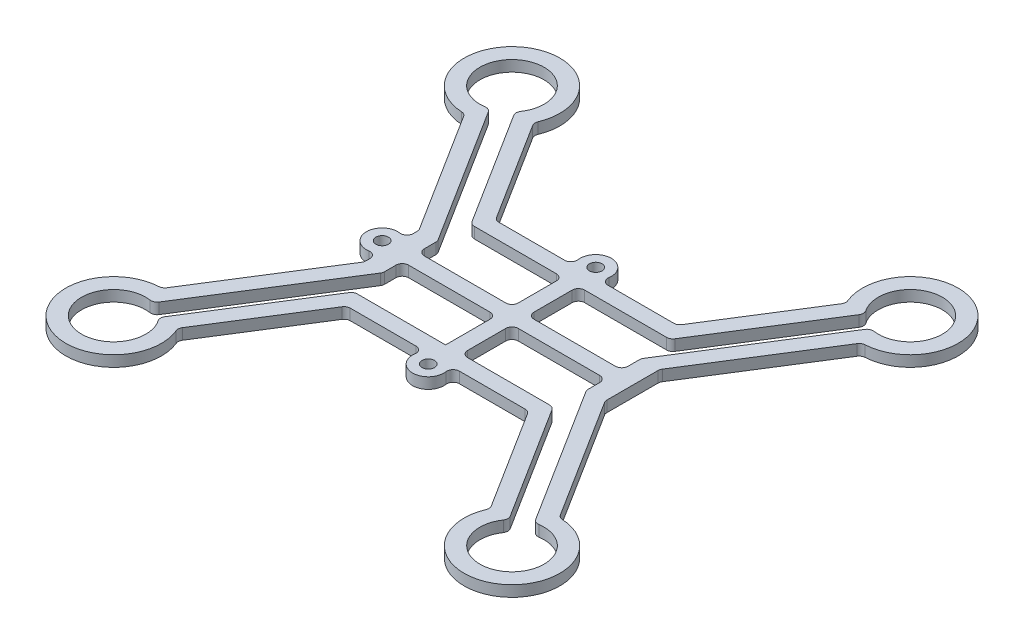
SolidWorks part; units mm, degrees
material "Hexcel AS4C (3000 Filaments)"
ref_plane "Front Plane" through (0, 0, 0) normal (0, 0, 1) x (1, 0, 0)
ref_plane "Top Plane" through (0, 0, 0) normal (0, 1, 0) x (1, 0, 0)
ref_plane "Right Plane" through (0, 0, 0) normal (1, 0, 0) x (0, 0, -1)
sketch "Sketch1" plane through (0, 0, 0) normal (0, 1, 0) x (1, 0, 0)
  line L0 (0, 28.7416) -> (0, -31.95) construction
  line L1 (-19.25, 11.875) -> (19.25, 11.875)
  line L2 (-19.25, 11.875) -> (-19.25, -11.875)
  line L3 (-19.25, -11.875) -> (19.25, -11.875)
  line L4 (19.25, 11.875) -> (19.25, -11.875)
  line L5 (-19.25, 11.875) -> (19.25, -11.875) construction
  line L6 (-19.25, -11.875) -> (19.25, 11.875) construction
  line L7 (-23.7954, 0) -> (45.7192, 0) construction
  line L8 (-31.8198, 4.3198) -> (-31.8198, -4.3198) construction
  line L9 (-31.8198, -31.8198) -> (-31.8198, 31.8198) construction
  line L10 (-31.8198, 31.8198) -> (-19.25, 11.875) construction
  line L11 (19.25, 9.825) -> (-13.5, 9.825)
  line L12 (19.25, 9.825) -> (19.25, -9.825)
  line L13 (19.25, -9.825) -> (-13.5, -9.825)
  line L14 (-13.5, 9.825) -> (-13.5, -9.825)
  line L15 (19.25, 9.825) -> (-13.5, -9.825) construction
  line L16 (19.25, -9.825) -> (-13.5, 9.825) construction
  line L17 (-31.727, 24.1704) -> (-19.25, 4.3728)
  line L18 (-24.959, 28.4358) -> (-14.5219, 11.875)
  line L19 (-35.2038, 29.6871) -> (-22.634, 9.7423) construction
  line L20 (-28.4358, 33.9525) -> (-15.866, 14.0077) construction
  line L21 (24.959, 28.4358) -> (14.5219, 11.875)
  line L22 (31.727, 24.1704) -> (19.25, 4.3728)
  line L23 (24.959, -28.4358) -> (14.5219, -11.875)
  line L24 (31.727, -24.1704) -> (19.25, -4.3728)
  line L25 (-24.959, -28.4358) -> (-14.5219, -11.875)
  line L26 (-31.727, -24.1704) -> (-19.25, -4.3728)
  line L27 (-31.8198, 31.8198) -> (31.8198, 31.8198) construction
  circle A0 centre (-31.8198, 31.8198) radius 27.5
  circle A1 centre (31.8198, 31.8198) radius 27.5
  circle A2 centre (-31.8198, -31.8198) radius 27.5
  circle A3 centre (31.8198, -31.8198) radius 27.5
  circle A4 centre (-31.8198, 31.8198) radius 7.65
  circle A5 centre (-31.8198, 31.8198) radius 5.125
  circle A6 centre (31.8198, 31.8198) radius 5.125
  circle A7 centre (31.8198, 31.8198) radius 7.65
  circle A8 centre (31.8198, -31.8198) radius 5.125
  circle A9 centre (31.8198, -31.8198) radius 7.65
  circle A10 centre (-31.8198, -31.8198) radius 5.125
  circle A11 centre (-31.8198, -31.8198) radius 7.65
  point P0 (0, 0)
  point P18 (2.875, 0)
  dimension "D3" = 55
  dimension "D8" = 15.3
  dimension "D9" = 10.25
  dimension "D1" = 23.75
  dimension "D2" = 38.5
  dimension "D4" = 19.65
  dimension "D5" = 32.75
  dimension "D10" = 8
  dimension "D6" = 90
extrude "Boss-Extrude1" add sketch "Sketch1" along normal blind 1.75 contours A4 A5 | A4 L17 L2 L1 L18 | A11 A10 | L26 A11 L25 L3 L2 | A9 A8 | A9 L24 L4 L3 L23 | A7 A6 | L22 A7 L21 L1 L4 | L26 A2 L2 | A0 L17 L2 | A3 L24 L4 | L22 A1 L12
sketch "Sketch2" plane through (0, 1.75, 0) normal (0, 1, 0) x (1, 0, 0)
  line L0 (-19.25, 0) -> (19.25, 0) construction
  line L1 (-19.25, 4.3728) -> (-19.25, -4.3728) construction
  line L2 (19.25, 4.3728) -> (19.25, -4.3728) construction
  line L3 (0, 11.875) -> (0, -11.875) construction
  line L4 (-14.5219, 11.875) -> (14.5219, 11.875) construction
  line L5 (-14.5219, -11.875) -> (14.5219, -11.875) construction
  line L6 (-29.0873, 27.484) -> (-11.766, 0) construction
  line L7 (-31.727, 24.1704) -> (-19.25, 4.3728) construction
  line L8 (-24.959, 28.4358) -> (-14.5219, 11.875) construction
  line L9 (-30.4507, 26.881) -> (-16.2654, 4.3728)
  line L10 (-31.8198, 36.9448) -> (-31.8198, 39.4698) construction
  line L11 (-23.3581, 15.6269) -> (-25.4942, 14.2807) construction
  line L12 (-19.25, 4.3728) -> (19.25, 4.3728) construction
  line L13 (-27.955, 28.4539) -> (-12.7784, 4.3728)
  line L14 (-15.9152, 9.35) -> (15.9152, 9.35)
  line L15 (0, 9.35) -> (0, 11.875) construction
  line L16 (-16.2654, 4.3728) -> (-16.2654, -4.3728)
  line L17 (-12.7784, 4.3728) -> (-12.7784, -4.3728)
  line L18 (12.7784, 4.3728) -> (12.7784, -4.3728)
  line L19 (16.2654, 4.3728) -> (16.2654, -4.3728)
  line L20 (27.955, 28.4539) -> (12.7784, 4.3728)
  line L21 (30.4507, 26.881) -> (16.2654, 4.3728)
  line L22 (27.955, -28.4539) -> (12.7784, -4.3728)
  line L23 (30.4507, -26.881) -> (16.2654, -4.3728)
  line L24 (-15.9152, -9.35) -> (15.9152, -9.35)
  line L25 (-30.4507, -26.881) -> (-16.2654, -4.3728)
  line L26 (-27.955, -28.4539) -> (-12.7784, -4.3728)
  line L27 (-1.2625, 0) -> (1.2625, 0) construction
  line L28 (1.2625, -9.35) -> (-1.2625, -9.35)
  line L29 (1.2625, -9.35) -> (1.2625, 9.35)
  line L30 (1.2625, 9.35) -> (-1.2625, 9.35)
  line L31 (-1.2625, -9.35) -> (-1.2625, 9.35)
  line L32 (1.2625, -9.35) -> (-1.2625, 9.35) construction
  line L33 (1.2625, 9.35) -> (-1.2625, -9.35) construction
  line L35 (-16.2654, -1.2625) -> (16.2654, -1.2625)
  line L36 (-16.2654, -1.2625) -> (-16.2654, 1.2625)
  line L37 (-16.2654, 1.2625) -> (16.2654, 1.2625)
  line L38 (16.2654, -1.2625) -> (16.2654, 1.2625)
  line L39 (-16.2654, -1.2625) -> (16.2654, 1.2625) construction
  line L40 (-16.2654, 1.2625) -> (16.2654, -1.2625) construction
  circle A0 centre (-31.8198, 31.8198) radius 5.125 construction
  circle A1 centre (-31.8198, 31.8198) radius 5.125
  circle A2 centre (31.8198, 31.8198) radius 5.125
  arc A3 (-24.959, 28.4358) -> (-31.727, 24.1704) centre (-31.8198, 31.8198) ccw construction
  circle A4 centre (-31.8198, -31.8198) radius 5.125
  circle A5 centre (31.8198, -31.8198) radius 5.125
  point P39 (0, 0)
  point P41 (0, 0)
  point P42 (-16.2654, 0)
  point P45 (12.7784, 0)
  point P47 (0, 9.35)
  point P60 (16.2654, 0)
  point P66 (-12.7784, 0)
extrude "Cut-Extrude2" cut sketch "Sketch2" against normal up to next contours L16 L37 L17 L13 L33 L9 | L17 L37 L31 L14 L13 | L29 L37 L18 L20 L14 | L18 L37 L19 L21 L36 L20 | L35 L18 L22 L23 L19 | L35 L29 L24 L22 L18 | L35 L17 L26 L24 L31 | L35 L16 L25 L32 L26 L17
fillet "Fillet1" radius 1 43 edges at (-30.4507, 0.875, 26.881) (-31.727, 0.875, -24.1704) (-1.2625, 0.875, -1.2625) (1.2625, 0.875, -1.2625) (-16.2654, 0.875, -1.2625) (-1.2625, 0.875, 1.2625) (-1.2625, 0.875, -9.35) (-31.727, 0.875, 24.1704) (-19.25, 0.875, 4.3728) (-19.25, 0.875, -4.3728) (24.959, 0.875, -28.4358) (-27.955, 0.875, -28.4539) (-27.955, 0.875, 28.4539) (-14.5219, 0.875, -11.875) (-15.9152, 0.875, 9.35) (-30.4507, 0.875, -26.881) (-24.959, 0.875, -28.4358) (-15.9152, 0.875, -9.35) (-16.2654, 0.875, -4.3728) (-16.2654, 0.875, 4.3728) (-16.2654, 0.875, 1.2625) (1.2625, 0.875, -9.35) (1.2625, 0.875, 1.2625) (1.2625, 0.875, 9.35) (16.2654, 0.875, -1.2625) (16.2654, 0.875, -4.3728) (15.9152, 0.875, -9.35) (14.5219, 0.875, -11.875) (30.4507, 0.875, -26.881) (27.955, 0.875, -28.4539) (31.727, 0.875, -24.1704) (19.25, 0.875, -4.3728) (16.2654, 0.875, 1.2625) (16.2654, 0.875, 4.3728) (15.9152, 0.875, 9.35) (19.25, 0.875, 4.3728) (31.727, 0.875, 24.1704) (30.4507, 0.875, 26.881) (27.955, 0.875, 28.4539) (24.959, 0.875, 28.4358) (14.5219, 0.875, 11.875) (-14.5219, 0.875, 11.875) (-24.959, 0.875, 28.4358)
sketch "Sketch4" plane through (0, 0, 0) normal (0, -1, 0) x (1, 0, 0)
  line L0 (-28.6014, 0) -> (31.9252, 0) construction
  line L1 (0, -23.8326) -> (0, 22.253) construction
  line L2 (-13.9701, -11.875) -> (13.9701, -11.875) construction
  line L3 (-0.866, -11.875) -> (-1.7321, -13.375)
  line L4 (-1.7321, -13.375) -> (-0.866, -14.875)
  line L5 (-0.866, -14.875) -> (0.866, -14.875)
  line L6 (0.866, -14.875) -> (1.7321, -13.375)
  line L7 (1.7321, -13.375) -> (0.866, -11.875)
  line L8 (0.866, -11.875) -> (-0.866, -11.875)
  line L9 (-2.5, -13.375) -> (-2.5, -11.875) construction
  line L10 (-20.75, -2.5) -> (-19.25, -2.5) construction
  line L11 (-19.25, -4.084) -> (-19.25, 4.084) construction
  circle A0 centre (0, -13.375) radius 1
  circle A1 centre (0, -13.375) radius 2.5
  circle A2 centre (0, -13.375) radius 1.5 construction
  circle A3 centre (0, 13.375) radius 2.5
  circle A4 centre (0, 13.375) radius 1
  circle A5 centre (-20.75, 0) radius 1
  circle A6 centre (-20.75, 0) radius 2.5
  circle A7 centre (20.75, 0) radius 1
  circle A8 centre (20.75, 0) radius 2.5
  dimension "D1" = 2
  dimension "D2" = 5
  dimension "D3" = 3
extrude "Boss-Extrude2" add sketch "Sketch4" against normal up to surface (1.75 mm away) contours A6 A5 | A1 L8 L7 L6 L5 L4 L3 | L7 L8 L3 L4 L5 L6 A0 | A3 A4 up to face at (16.0204, 1.75, -12.188)
fillet "Fillet2" radius 1 6 edges at (2, 0.875, 11.875) (-2, 0.875, 11.875) (2, 0.875, -11.875) (-2, 0.875, -11.875) (-19.25, 0.875, 2) (-19.25, 0.875, -2)
equation "\"PropDiameter\"=55"
equation "\"D3@Sketch1\"=\"PropDiameter\""
